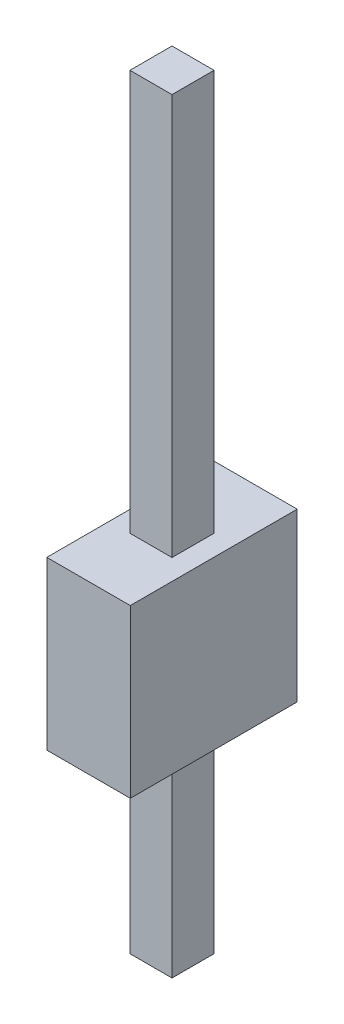
SolidWorks part; units mm, degrees
ref_plane "Front Plane" through (0, 0, 0) normal (0, 0, 1) x (1, 0, 0)
ref_plane "Top Plane" through (0, 0, 0) normal (0, 1, 0) x (1, 0, 0)
ref_plane "Right Plane" through (0, 0, 0) normal (1, 0, 0) x (0, 0, -1)
sketch "Sketch1" plane through (0, 0, 0) normal (0, 1, 0) x (1, 0, 0)
  line L1 (0, 0) -> (1.27, 0)
  line L2 (0, 0) -> (0, 2.54)
  line L3 (0, 2.54) -> (1.27, 2.54)
  line L4 (1.27, 0) -> (1.27, 2.54)
  dimension "D1" = 1.27
  dimension "D2" = 2.54
extrude "Boss-Extrude1" add sketch "Sketch1" along normal blind 2.54
sketch "Sketch2" plane through (0, 2.54, 0) normal (0, 1, 0) x (1, 0, 0)
  line L0 (0.635, 2.54) -> (0.635, 1.59) construction
  line L1 (0.315, 1.59) -> (0.955, 1.59)
  line L2 (0.315, 1.59) -> (0.315, 0.95)
  line L3 (0.315, 0.95) -> (0.955, 0.95)
  line L4 (0.955, 1.59) -> (0.955, 0.95)
  line L5 (1.27, 2.54) -> (0, 2.54) construction
  line L6 (0, 1.27) -> (0.315, 1.27) construction
  line L7 (0, 2.54) -> (0, 0) construction
  point P12 (0.315, 1.27)
  point P13 (0.635, 1.59)
  dimension "D1" = 0.64
extrude "Boss-Extrude2" add sketch "Sketch2" along normal blind 6.1 and the other way offset from surface (5.54 mm away) 3 other way up to face at (0.635, 0, -1.27)
